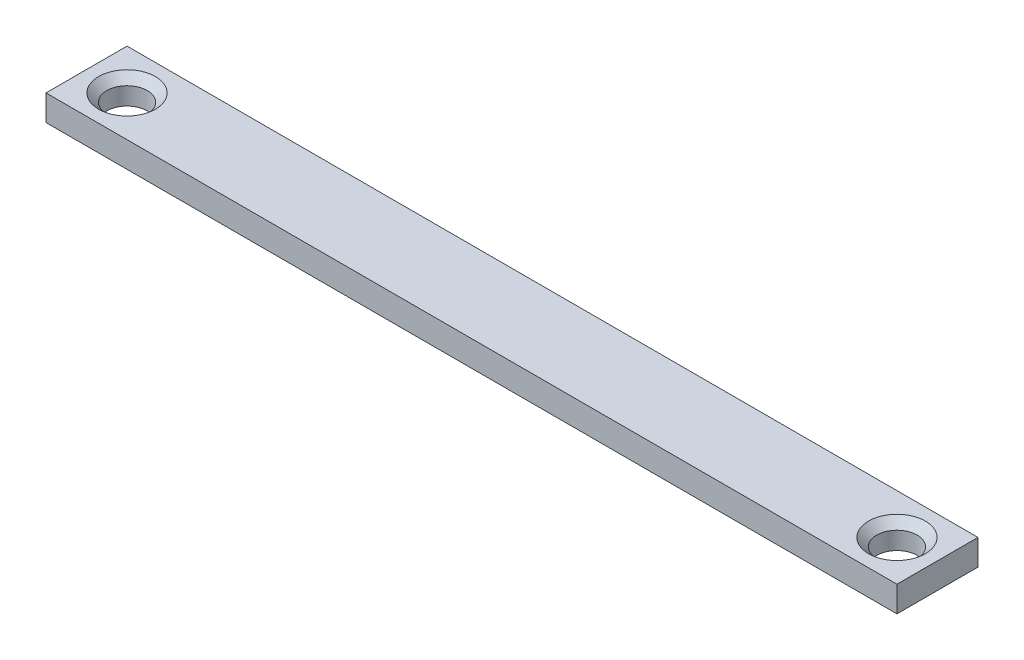
SolidWorks part; units mm, degrees
ref_plane "Front Plane" through (0, 0, 0) normal (0, 0, 1) x (1, 0, 0)
ref_plane "Top Plane" through (0, 0, 0) normal (0, 1, 0) x (1, 0, 0)
ref_plane "Right Plane" through (0, 0, 0) normal (1, 0, 0) x (0, 0, -1)
sketch "Sketch1" plane through (0, 0, 0) normal (0, 1, 0) x (1, 0, 0)
  line L1 (-52.5, -5) -> (52.5, -5)
  line L2 (-52.5, -5) -> (-52.5, 5)
  line L3 (-52.5, 5) -> (52.5, 5)
  line L4 (52.5, -5) -> (52.5, 5)
  line L5 (-52.5, -5) -> (52.5, 5) construction
  line L6 (-52.5, 5) -> (52.5, -5) construction
  point P0 (0, 0)
  dimension "D1" = 105
  dimension "D2" = 10
extrude "Boss-Extrude1" add sketch "Sketch1" along normal blind 3.175
sketch "Sketch2" plane through (0, 3.175, 0) normal (0, 1, 0) x (1, 0, 0)
  line L0 (-47.5, 0) -> (47.5, 0) construction
  circle A0 centre (-47.5, 0) radius 3
  circle A1 centre (47.5, 0) radius 3
  point P0 (-47.5, 0)
  point P2 (47.5, 0)
  point P9 (-47.5, 0)
  point P12 (47.5, 0)
  point P15 (0, 0)
  point P18 (-47.5, 0)
  point P22 (-47.5, 0)
  point P24 (-47.5, 0)
  point P26 (47.5, 0)
  dimension "D1" = 6
  dimension "D2" = 6
  dimension "D3" = 95
hole_wizard "M6x1.0 Tapped Hole1" positions "Sketch2" profile "Sketch4" tap size "M6x1.0" standard "ANSI Metric"
sketch "Sketch4" plane through (47.5, 3.175, 0) normal (1, 0, 0) x (0, 0, 1)
  line L0 (0, 0) -> (0, 3.175)
  line L1 (0, 3.175) -> (2.5, 3.175)
  line L2 (2.5, 3.175) -> (2.5, 1)
  line L3 (2.5, 1) -> (3.5, 0)
  line L5 (3.5, 0) -> (0, 0)
  line L6 (-2.5, 1) -> (-3.5, 0) construction
  line L11 (0, -6.35) -> (0, 107.95) construction
  dimension "Thru Tap Drill Dia." = 5
  dimension "Thru Tap Drill Depth" = 3.175
  dimension "Near C'Sink Dia." = 7
  dimension "Near C'Sink Angle" = 90
